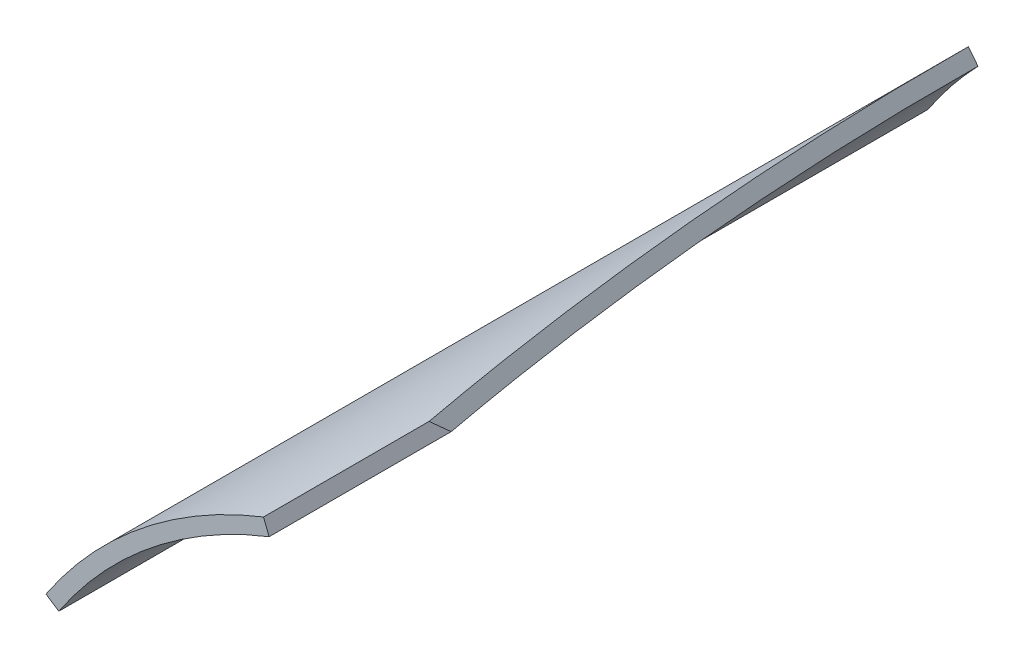
SolidWorks part; units mm, degrees
ref_plane "Front Plane" through (0, 0, 0) normal (0, 0, 1) x (1, 0, 0)
ref_plane "Top Plane" through (0, 0, 0) normal (0, 1, 0) x (1, 0, 0)
ref_plane "Right Plane" through (0, 0, 0) normal (1, 0, 0) x (0, 0, -1)
sketch "Sketch1" plane through (0, 0, 0) normal (0, 0, 1) x (1, 0, 0)
  line L0 (0, 76) -> (0, 78.6)
  line L1 (0, -76) -> (0, -78.6)
  arc A0 (0, 78.6) -> (0, -78.6) centre (0, 0) ccw
  arc A1 (0, 76) -> (0, -76) centre (0, 0) ccw
  dimension "D1" = 152
  dimension "D2" = 157.2
extrude "Boss-Extrude1" add sketch "Sketch1" against normal blind 147 from offset 392 offset against normal yes
sketch "Sketch2" plane through (0, 0, -392) normal (0, 0, 1) x (1, 0, 0)
  line L0 (0, 0) -> (-28.6793, 73.181)
  line L1 (0, 0) -> (-65.4676, 43.4966)
  line L2 (0, 0) -> (0, 53.2709) construction
  arc A0 (-65.4676, 43.4966) -> (-28.6793, 73.181) centre (0, 0) ccw
  arc A1 (0, 78.6) -> (0, -78.6) centre (0, 0) ccw construction
  dimension "D1" = 21.4
  dimension "D2" = 56.4
extrude "Cut-Extrude1" cut sketch "Sketch2" against normal through all
ref_plane "Plane1" through (-45.5163, 56.409, 0) normal (-0.628, 0.7782, 0) x (0.7782, 0.628, 0)
sketch "Sketch3" plane through (-45.5163, 56.409, 0) normal (-0.628, 0.7782, 0) x (0.7782, 0.628, 0)
  line L1 (23.6355, 392) -> (-97.8181, 392)
  line L2 (-97.8181, 392) -> (-57.3203, 551.1351)
  line L3 (-57.3203, 551.1351) -> (-9.6355, 539)
  line L4 (23.6355, 392) -> (23.6355, 420)
  line L5 (23.6355, 539) -> (-23.6355, 539) construction
  line L6 (-9.6355, 539) -> (23.6355, 420)
  dimension "D1" = 28
  dimension "D2" = 14
extrude "Cut-Extrude2" cut sketch "Sketch3" against normal through all and the other way through all flip side to cut
